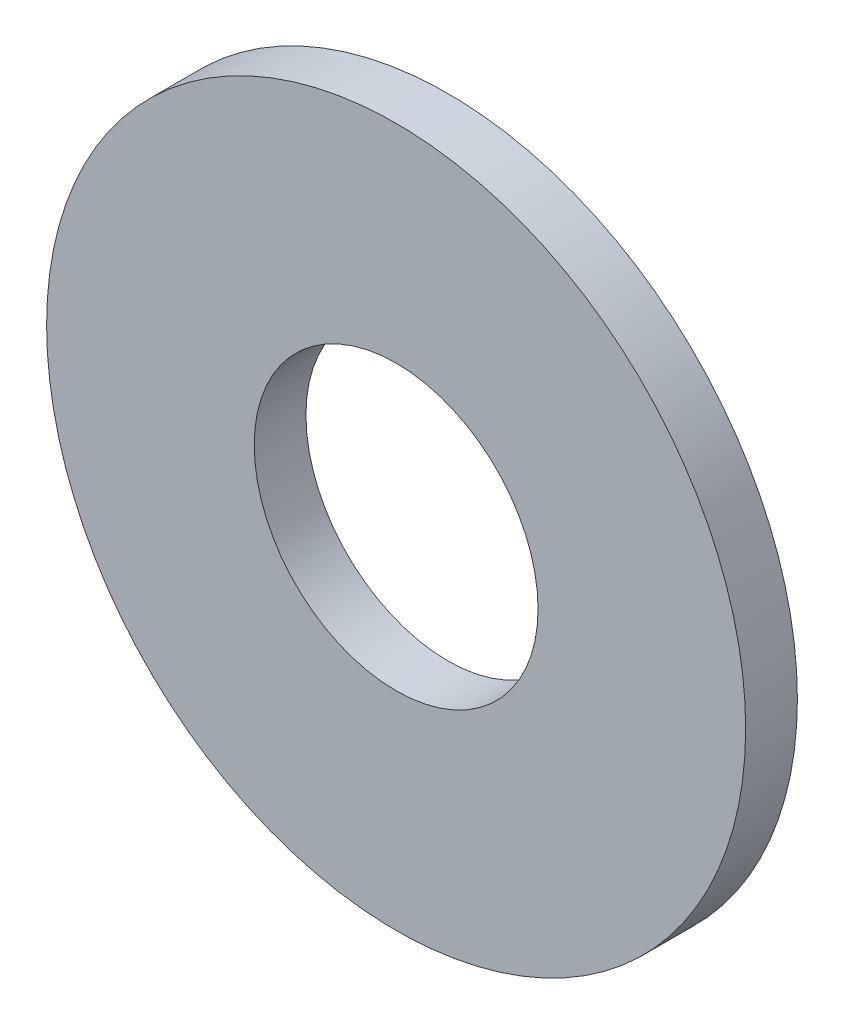
SolidWorks part; units mm, degrees
ref_plane "Front Plane" through (0, 0, 0) normal (0, 0, 1) x (1, 0, 0)
ref_plane "Top Plane" through (0, 0, 0) normal (0, 1, 0) x (1, 0, 0)
ref_plane "Right Plane" through (0, 0, 0) normal (1, 0, 0) x (0, 0, -1)
sketch "Sketch1" plane through (0, 0, 0) normal (1, 0, 0) x (0, 0, -1)
  line L0 (-34.925, 0) -> (9.525, 0) construction
  line L1 (0, 10.3124) -> (0, 25.4)
  line L2 (0, 25.4) -> (-3.7592, 25.4)
  line L3 (-3.7592, 25.4) -> (-3.7592, 10.3124)
  line L4 (-3.7592, 10.3124) -> (0, 10.3124)
  dimension "Thickness" = 3.7592
  dimension "Inside_dia" = 20.6248
  dimension "Outside_dia" = 50.8
revolve "Revolve1" add sketch "Sketch1" angle 360 about L0
